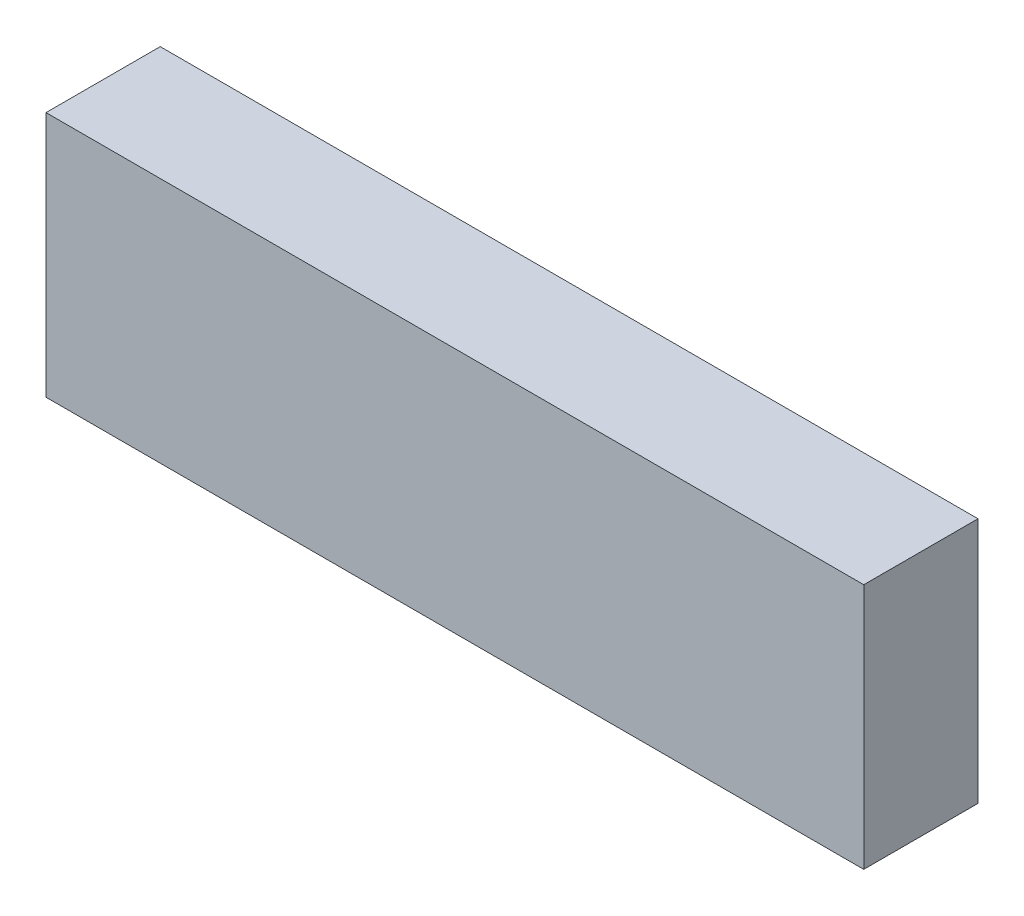
SolidWorks part; units mm, degrees
ref_plane "Front Plane" through (0, 0, 0) normal (0, 0, 1) x (1, 0, 0)
ref_plane "Top Plane" through (0, 0, 0) normal (0, 1, 0) x (1, 0, 0)
ref_plane "Right Plane" through (0, 0, 0) normal (1, 0, 0) x (0, 0, -1)
sketch "Эскиз1" plane through (0, 0, 0) normal (0, 0, 1) x (1, 0, 0)
  line L1 (-68, -20.5) -> (68, -20.5)
  line L2 (-68, -20.5) -> (-68, 20.5)
  line L3 (-68, 20.5) -> (68, 20.5)
  line L4 (68, -20.5) -> (68, 20.5)
  line L5 (-68, -20.5) -> (68, 20.5) construction
  line L6 (-68, 20.5) -> (68, -20.5) construction
  point P0 (0, 0)
  dimension "D1" = 136
  dimension "D2" = 41
extrude "Бобышка-Вытянуть1" add sketch "Эскиз1" along normal mid plane 19
